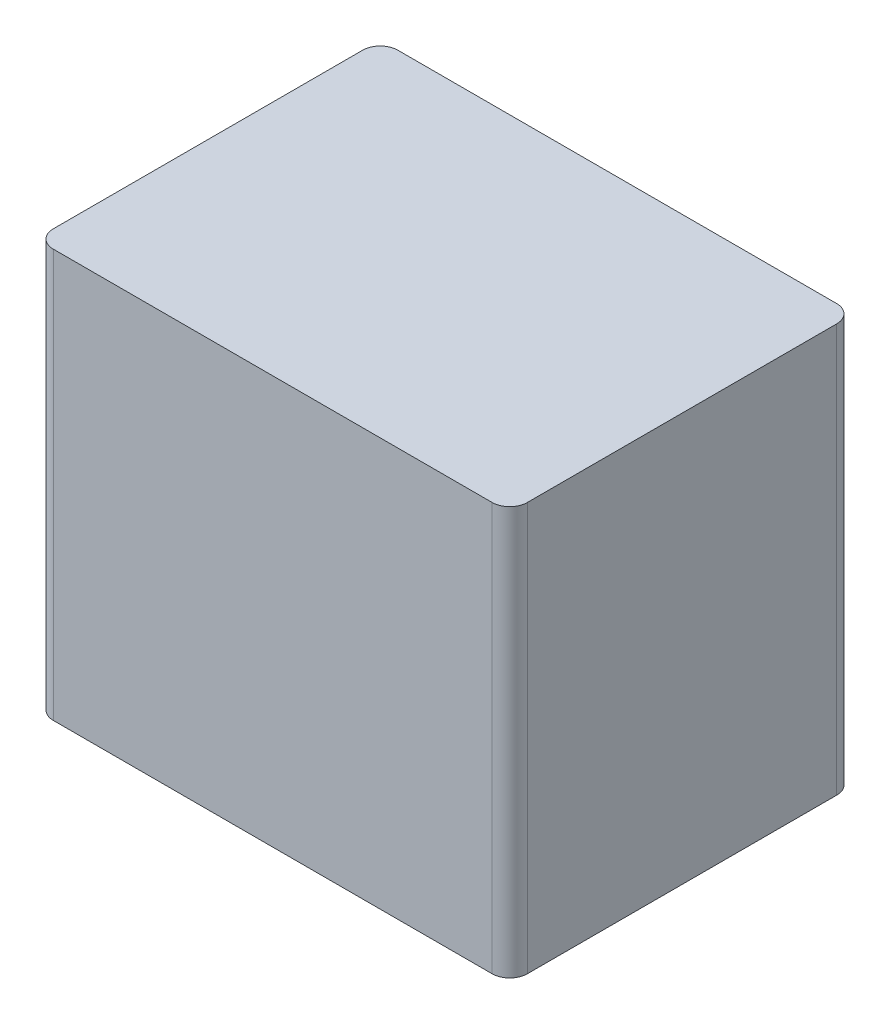
SolidWorks part; units mm, degrees
ref_plane "Front Plane" through (0, 0, 0) normal (0, 0, 1) x (1, 0, 0)
ref_plane "Top Plane" through (0, 0, 0) normal (0, 1, 0) x (1, 0, 0)
ref_plane "Right Plane" through (0, 0, 0) normal (1, 0, 0) x (0, 0, -1)
sketch "Sketch1" plane through (0, 0, 0) normal (0, 1, 0) x (1, 0, 0)
  line L1 (0, 0) -> (54, 0)
  line L2 (0, 0) -> (0, 39.25)
  line L3 (0, 39.25) -> (54, 39.25)
  line L4 (54, 0) -> (54, 39.25)
  dimension "D1" = 54
  dimension "D2" = 39.25
extrude "Boss-Extrude1" add sketch "Sketch1" along normal blind 46.5
fillet "Fillet1" radius 2 1 edges at (0, 23.25, 0)
fillet "Fillet2" radius 2 3 edges at (54, 23.25, -39.25) (54, 23.25, 0) (0, 23.25, -39.25)
